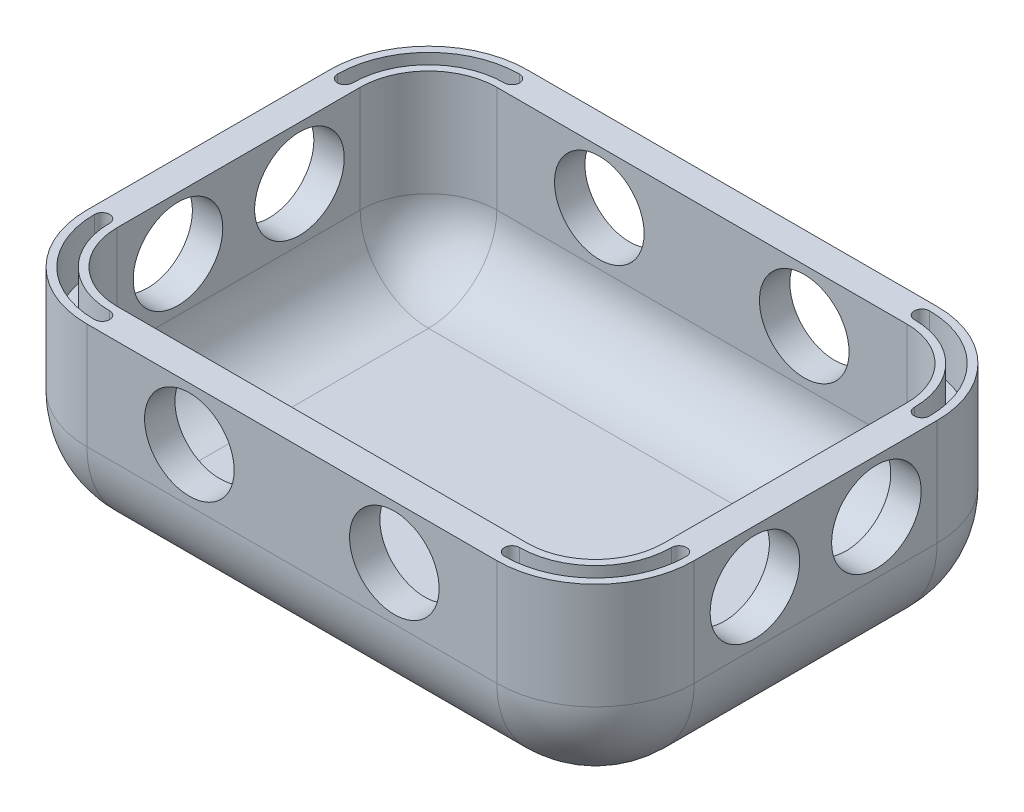
SolidWorks part; units mm, degrees
material "ABS"
ref_plane "Front Plane" through (0, 0, 0) normal (0, 0, 1) x (1, 0, 0)
ref_plane "Top Plane" through (0, 0, 0) normal (0, 1, 0) x (1, 0, 0)
ref_plane "Right Plane" through (0, 0, 0) normal (1, 0, 0) x (0, 0, -1)
sketch "Sketch1" plane through (0, 0, 0) normal (0, 1, 0) x (1, 0, 0)
  line L1 (-20, 14.5) -> (20, 14.5)
  line L2 (-20, 14.5) -> (-20, -14.5)
  line L3 (-20, -14.5) -> (20, -14.5)
  line L4 (20, 14.5) -> (20, -14.5)
  line L5 (0, -14.5) -> (0, 14.5) construction
  line L6 (-20, 0) -> (20, 0) construction
  point P0 (0, 0)
  dimension "D1" = 29
  dimension "D2" = 40
extrude "Boss-Extrude1" add sketch "Sketch1" along normal blind 20
fillet "Fillet2" radius 6.5 12 edges at (0, 20, 14.5) (-20, 20, 0) (0, 20, -14.5) (20, 20, 0) (0, 0, -14.5) (-20, 0, 0) (0, 0, 14.5) (20, 0, 0) (20, 10, 14.5) (20, 10, -14.5) (-20, 10, -14.5) (-20, 10, 14.5)
ref_plane "Plane3" through (0, 13.5, 0) normal (0, 1, 0) x (1, 0, 0)
sketch "Sketch6" plane through (0, 13.5, 0) normal (0, 1, 0) x (1, 0, 0)
  line L1 (23.9331, -17.9116) -> (-23.9331, -17.9116)
  line L2 (23.9331, -17.9116) -> (23.9331, 17.9116)
  line L3 (23.9331, 17.9116) -> (-23.9331, 17.9116)
  line L4 (-23.9331, -17.9116) -> (-23.9331, 17.9116)
  line L5 (0, 17.9116) -> (0, -17.9116) construction
  line L6 (23.9331, 0) -> (-23.9331, 0) construction
  point P0 (0, 0)
extrude "Cut-Extrude6" cut sketch "Sketch6" along normal through all
shell "Shell1" thickness 2
sketch "Sketch7" plane through (20, 0, 0) normal (1, 0, 0) x (0, 0, -1)
  line L0 (0, 6.5) -> (8, 10) construction
  line L3 (-8, 6.5) -> (8, 6.5) construction
  line L4 (8, 6.5) -> (8, 13.5) construction
  line L5 (8, 10) -> (0, 10) construction
  line L6 (0, 10) -> (-8, 10) construction
  line L7 (-8, 13.5) -> (-8, 6.5) construction
  line L8 (0, 6.5) -> (0, 10) construction
  circle A0 centre (4, 10) radius 2.95
  circle A1 centre (-4, 10) radius 2.95
  point P13 (4, 10)
  dimension "D1" = 5.9
extrude "Cut-Extrude7" cut sketch "Sketch7" against normal through all and the other way through all
sketch "Sketch8" plane through (0, 0, 14.5) normal (0, 0, 1) x (1, 0, 0)
  line L0 (-13.5, 10) -> (0, 10) construction
  line L1 (-13.5, 13.5) -> (-13.5, 6.5) construction
  line L2 (0, 10) -> (0, 6.5) construction
  line L3 (-13.5, 6.5) -> (13.5, 6.5) construction
  circle A0 centre (-6.75, 10) radius 2.95
  circle A1 centre (6.75, 10) radius 2.95
  dimension "D1" = 5.9
extrude "Cut-Extrude8" cut sketch "Sketch8" against normal through all
sketch "Sketch10" plane through (0, 13.5, 0) normal (0, 1, 0) x (1, 0, 0)
  line L8 (13.5, 14) -> (-13.5, 14)
  line L9 (-19.5, 8) -> (-19.5, -8)
  line L10 (-13.5, -14) -> (13.5, -14)
  line L11 (19.5, -8) -> (19.5, 8)
  arc A4 (-18.5, -8) -> (-13.5, -13) centre (-13.5, -8) ccw
  arc A5 (-13.5, 13) -> (-18.5, 8) centre (-13.5, 8) ccw
  arc A6 (18.5, 8) -> (13.5, 13) centre (13.5, 8) ccw
  arc A7 (13.5, -13) -> (18.5, -8) centre (13.5, -8) ccw
  arc A8 (-13.5, 14) -> (-19.5, 8) centre (-13.5, 8) ccw
  arc A9 (-19.5, -8) -> (-13.5, -14) centre (-13.5, -8) ccw
  arc A10 (13.5, -14) -> (19.5, -8) centre (13.5, -8) ccw
  arc A11 (19.5, 8) -> (13.5, 14) centre (13.5, 8) ccw
  arc A12 (-13.5, 14) -> (-19.5, 8) centre (-13.5, 8) ccw
  arc A13 (-19.5, -8) -> (-13.5, -14) centre (-13.5, -8) ccw
  arc A14 (13.5, -14) -> (19.5, -8) centre (13.5, -8) ccw
  arc A15 (19.5, 8) -> (13.5, 14) centre (13.5, 8) ccw
  arc A16 (-19.5, -8) -> (-18.5, -8) centre (-19, -8) cw
  arc A17 (-13.5, -14) -> (-13.5, -13) centre (-13.5, -13.5) ccw
  arc A18 (-13.5, 14) -> (-13.5, 13) centre (-13.5, 13.5) cw
  arc A19 (-19.5, 8) -> (-18.5, 8) centre (-19, 8) ccw
  arc A20 (19.5, 8) -> (18.5, 8) centre (19, 8) cw
  arc A21 (13.5, 14) -> (13.5, 13) centre (13.5, 13.5) ccw
  arc A22 (13.5, -14) -> (13.5, -13) centre (13.5, -13.5) cw
  arc A23 (19.5, -8) -> (18.5, -8) centre (19, -8) ccw
  dimension "D1" = 0.5
  dimension "D2" = 1
extrude "Cut-Extrude10" cut sketch "Sketch10" against normal blind 3.3
